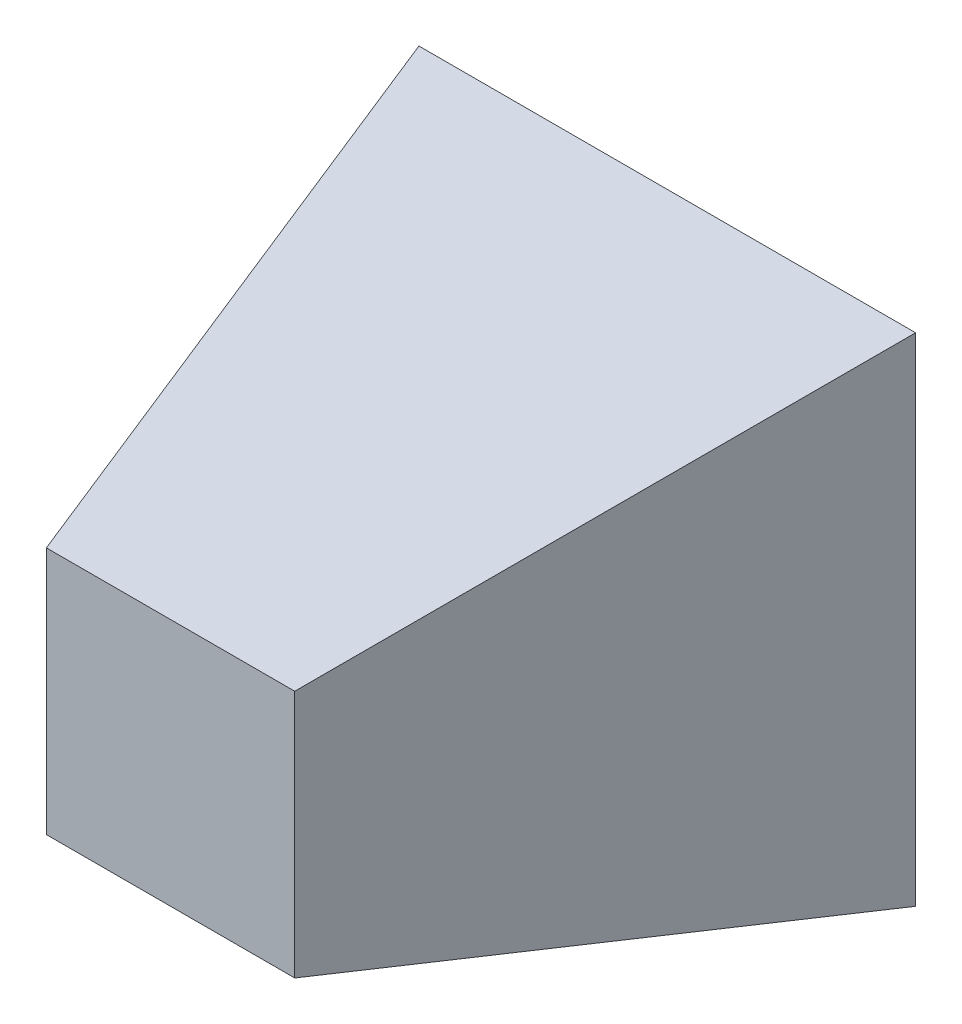
SolidWorks part; units mm, degrees
ref_plane "Front Plane" through (0, 0, 0) normal (0, 0, 1) x (1, 0, 0)
ref_plane "Top Plane" through (0, 0, 0) normal (0, 1, 0) x (1, 0, 0)
ref_plane "Right Plane" through (0, 0, 0) normal (1, 0, 0) x (0, 0, -1)
sketch "Sketch1" plane through (0, 0, 0) normal (0, 0, 1) x (1, 0, 0)
  line L1 (-50, 50) -> (50, 50)
  line L2 (-50, 50) -> (-50, -50)
  line L3 (-50, -50) -> (50, -50)
  line L4 (50, 50) -> (50, -50)
  line L5 (-50, 50) -> (50, -50) construction
  line L6 (-50, -50) -> (50, 50) construction
  point P0 (0, 0)
  dimension "D1" = 100
  dimension "D2" = 100
ref_plane "Plane1" through (0, 0, 100) normal (0, 0, 1) x (1, 0, 0)
sketch "Sketch2" plane through (0, 0, 100) normal (0, 0, 1) x (1, 0, 0)
  line L1 (-25, 25) -> (25, 25)
  line L2 (-25, 25) -> (-25, -25)
  line L3 (-25, -25) -> (25, -25)
  line L4 (25, 25) -> (25, -25)
  line L5 (-25, 25) -> (25, -25) construction
  line L6 (-25, -25) -> (25, 25) construction
  point P1 (0, 0)
  dimension "D1" = 50
  dimension "D2" = 50
loft "Loft1" add profiles "Sketch1", "Sketch2"
